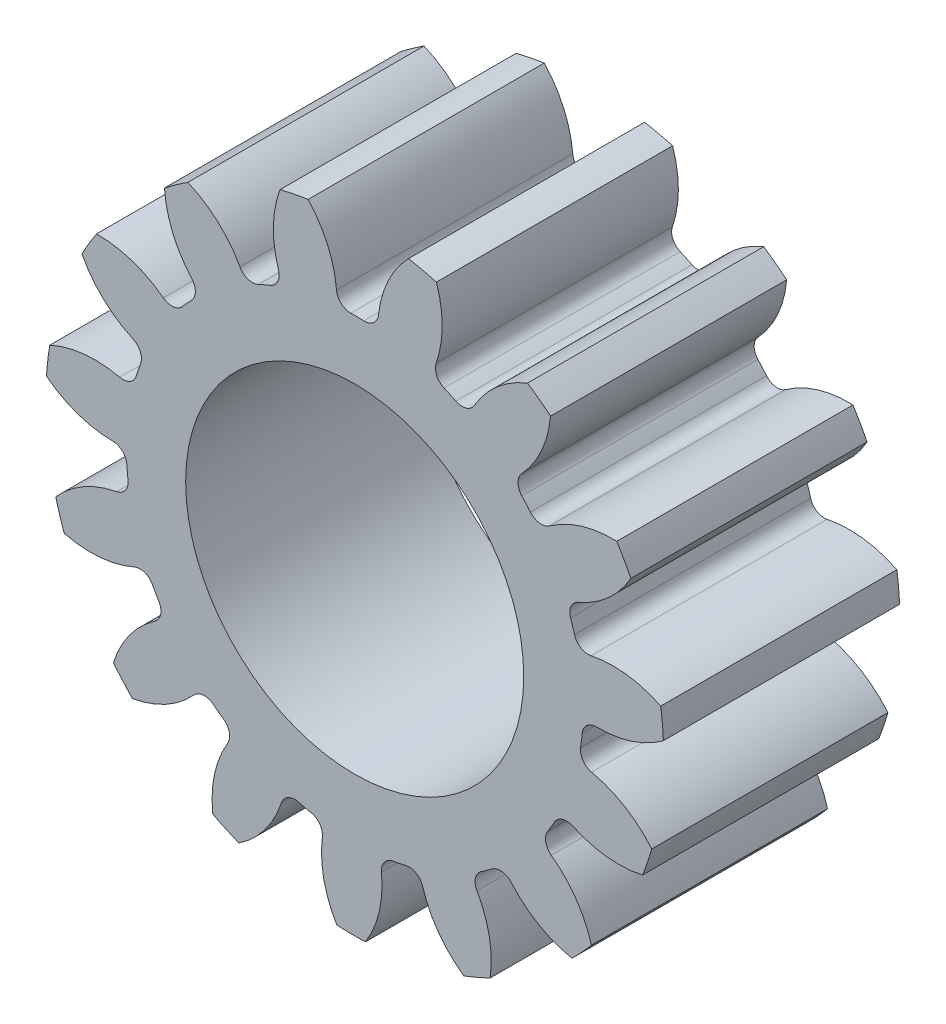
SolidWorks part; units mm, degrees
material "ABS"
ref_plane "Front" through (0, 0, 0) normal (0, 0, 1) x (1, 0, 0)
ref_plane "Top" through (0, 0, 0) normal (0, 1, 0) x (1, 0, 0)
ref_plane "Right" through (0, 0, 0) normal (1, 0, 0) x (0, 0, -1)
sketch "Sketch3" plane through (0, 0, 0) normal (0, 0, 1) x (1, 0, 0)
  circle A0 centre (0, 0) radius 21.59
  dimension "od" = 43.18
extrude "gearBody" add sketch "Sketch3" along normal blind 11
sketch "Sketch2" plane through (0, 0, 0) normal (0, 0, 1) x (1, 0, 0)
  line L0 (0, 0) -> (17.0393, 7.0579) construction
  line L1 (22.0105, -8.0941) -> (0, 0) construction
  line L2 (0, 0) -> (36.3143, 0) construction
  line L3 (19.0486, -0.229) -> (18.5878, -4.1711) construction
  line L5 (18.8182, -2.2) -> (0, 0) construction
  line L7 (0, 0) -> (18.4432, 0) construction
  arc A0 (18.4395, -0.3701) -> (18.0276, -3.8932) centre (0, 0) ccw construction
  arc A1 (21.5666, 1.0048) -> (20.7532, -5.9524) centre (0, 0) ccw construction
  arc A2 (19.0486, -0.229) -> (18.5878, -4.1711) centre (0, 0) ccw construction
  arc A3 (15.7838, -2.3046) -> (15.8898, -1.3984) centre (0, 0) ccw
  arc A4 (22.0105, -8.0941) -> (16.5506, -3.4102) centre (14.9518, -10.798) ccw
  arc A5 (22.0105, -8.0941) -> (23.2839, 2.7987) centre (0, 0) ccw
  arc A6 (23.2839, 2.7987) -> (16.8909, -0.4995) centre (17.0393, 7.0579) cw
  arc A7 (15.8898, -1.3984) -> (16.8909, -0.4995) centre (16.8715, -1.4848) cw
  arc A8 (16.5506, -3.4102) -> (15.7838, -2.3046) centre (16.759, -2.4469) cw
  arc A9 (23.6165, 5.3439) -> (16.9058, 0.2624) centre (17.0393, 7.0579) cw
  arc A10 (15.1307, -1.3316) -> (16.9058, 0.2624) centre (16.8715, -1.4848) cw
  arc A11 (15.0298, -2.1945) -> (15.1307, -1.3316) centre (0, 0) ccw
  arc A12 (16.3894, -4.1549) -> (15.0298, -2.1945) centre (16.759, -2.4469) cw
  arc A13 (21.747, -10.6473) -> (16.3894, -4.1549) centre (14.9518, -10.798) ccw
  arc A14 (21.747, -10.6473) -> (23.6165, 5.3439) centre (0, 0) ccw
  point P6 (23.2839, 2.7987)
  point P22 (22.0105, -8.0941)
  dimension "D1" = 0.762
  dimension "baseDia" = 36.8864
  dimension "od" = 43.18
  dimension "pd" = 38.1
  dimension "rd" = 31.9024
  dimension "rFillet" = 0.9855
  dimension "pointX" = 23.2839
  dimension "pointY" = 2.7987
  dimension "CTT" = 3.9421
  dimension "flankCenterAngle" = 22.5
extrude "toothCut" cut sketch "Sketch2" along normal through all contours A8 A4 A5 A6 A7 A3
pattern_circular "CirPattern1" count 15 over 360 about axis through (0, 0, 0) along (0, 0, 1) of "toothCut"
scale "Scale1" scale about centroid uniform scaling no x scale factor 0.666667 y scale factor 0.666667 z scale factor 1
sketch "hub1Dia" plane through (0, 0, 0) normal (0, 0, -1) x (-1, 0, 0)
  circle A0 centre (0, 0) radius 12.7
  dimension "hub1Dia" = 25.4
sketch "hub2Dia" plane through (0, 0, 11) normal (0, 0, 1) x (1, 0, 0)
  circle A0 centre (0, 0) radius 12.7
  dimension "hub2dia" = 25.4
sketch "boreDia" plane through (0, 0, 0) normal (0, 0, 1) x (1, 0, 0)
  circle A0 centre (0, 0) radius 7.874
  dimension "boreDia" = 15.748
extrude "bore" cut sketch "boreDia" against normal mid plane 25400
